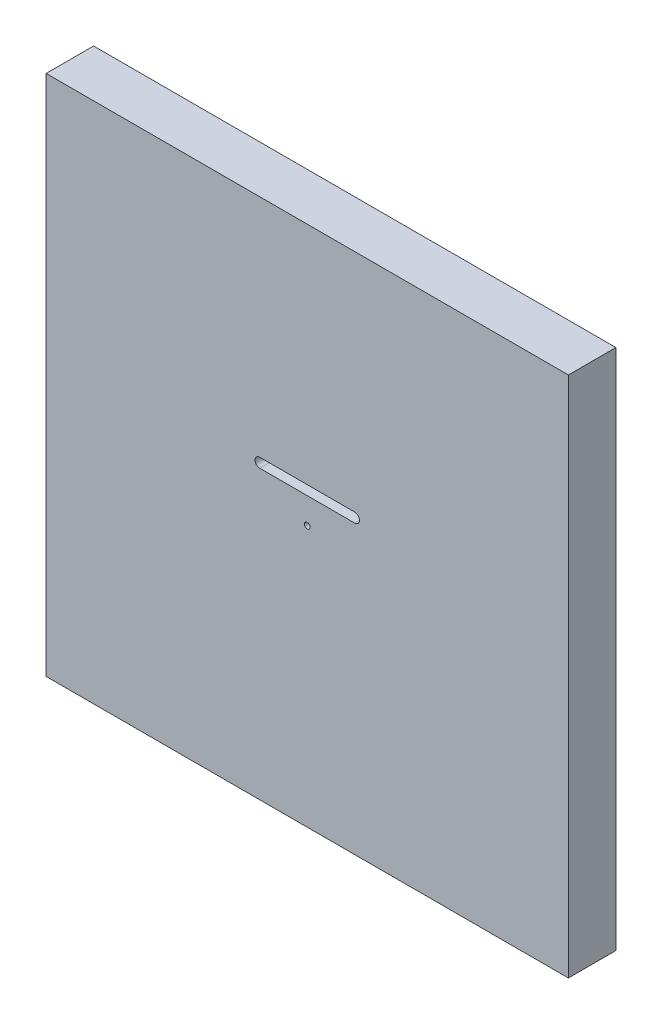
SolidWorks part; units mm, degrees
ref_plane "Alzado" through (0, 0, 0) normal (0, 0, 1) x (1, 0, 0)
ref_plane "Planta" through (0, 0, 0) normal (0, 1, 0) x (1, 0, 0)
ref_plane "Vista lateral" through (0, 0, 0) normal (1, 0, 0) x (0, 0, -1)
sketch "Croquis1" plane through (0, 0, 0) normal (0, 0, 1) x (1, 0, 0)
  line L1 (-234.0113, 178.5857) -> (315.9887, 178.5857)
  line L2 (-234.0113, 178.5857) -> (-234.0113, -371.4143)
  line L3 (-234.0113, -371.4143) -> (315.9887, -371.4143)
  line L4 (315.9887, 178.5857) -> (315.9887, -371.4143)
  dimension "D1" = 550
  dimension "D2" = 550
extrude "Saliente-Extruir1" add sketch "Croquis1" along normal blind 50
sketch "Croquis2" plane through (0, 0, 0) normal (0, 0, -1) x (-1, 0, 0)
  line L0 (234.0113, -371.4143) -> (-315.9887, -371.4143) construction
  line L1 (-90.9887, -58.9995) -> (9.0113, -58.9995)
  line L3 (-90.9887, -68.9995) -> (9.0113, -68.9995)
  arc A0 (-90.9887, -68.9995) -> (-90.9887, -58.9995) centre (-90.9887, -63.9995) cw
  arc A1 (9.0113, -68.9995) -> (9.0113, -58.9995) centre (9.0113, -63.9995) ccw
  circle A2 centre (-40.9887, -96.4143) radius 3
  point P6 (-40.9887, -371.4143)
  point P7 (-40.9887, -68.9995)
  dimension "D1" = 100
  dimension "D2" = 10
extrude "Cortar-Extruir1" cut sketch "Croquis2" against normal up to vertex (50 mm away)
